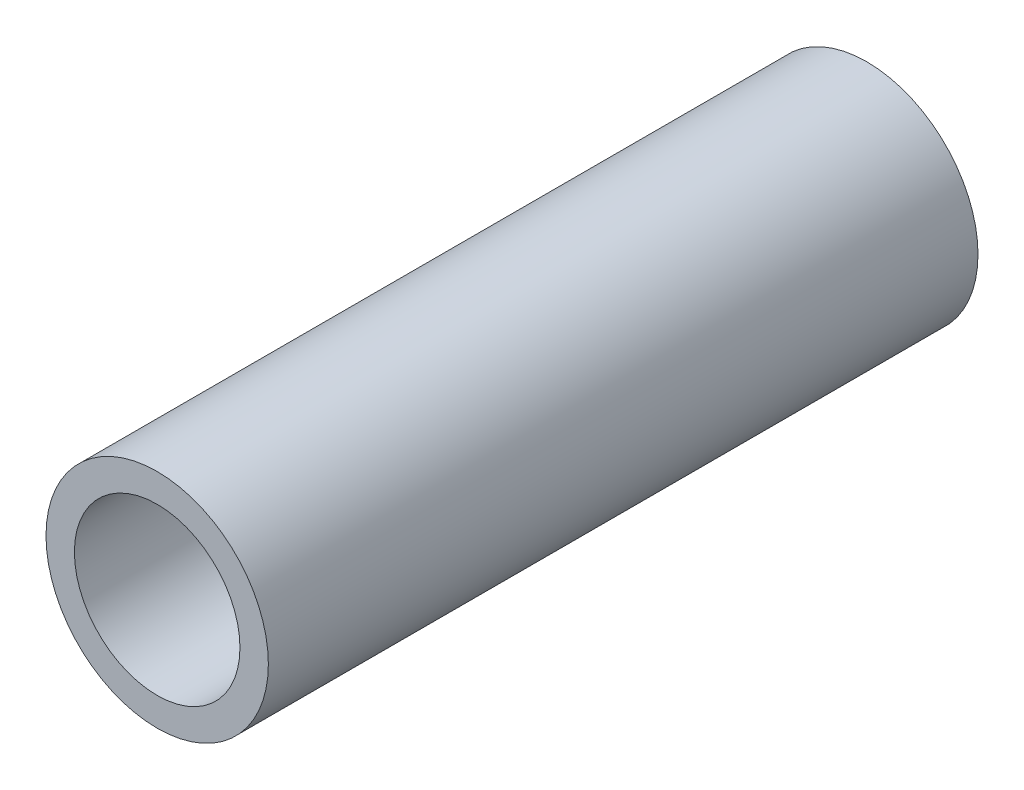
SolidWorks part; units mm, degrees
material "AISI Type 316L stainless steel"
ref_plane "Front Plane" through (0, 0, 0) normal (0, 0, 1) x (1, 0, 0)
ref_plane "Top Plane" through (0, 0, 0) normal (0, 1, 0) x (1, 0, 0)
ref_plane "Right Plane" through (0, 0, 0) normal (1, 0, 0) x (0, 0, -1)
sketch "Sketch1" plane through (0, 0, 0) normal (0, 0, 1) x (1, 0, 0)
  circle A0 centre (0, 0) radius 5.969
  dimension "D1" = 11.938
extrude "Boss-Extrude1" add sketch "Sketch1" along normal blind 38.1
sketch "Sketch2" plane through (0, 0, 38.1) normal (0, 0, 1) x (1, 0, 0)
  circle A0 centre (0, 0) radius 4.445
  circle A1 centre (0, 0) radius 5.969 construction
  dimension "D1" = 1.524
extrude "Cut-Extrude1" cut sketch "Sketch2" against normal blind 38.1
